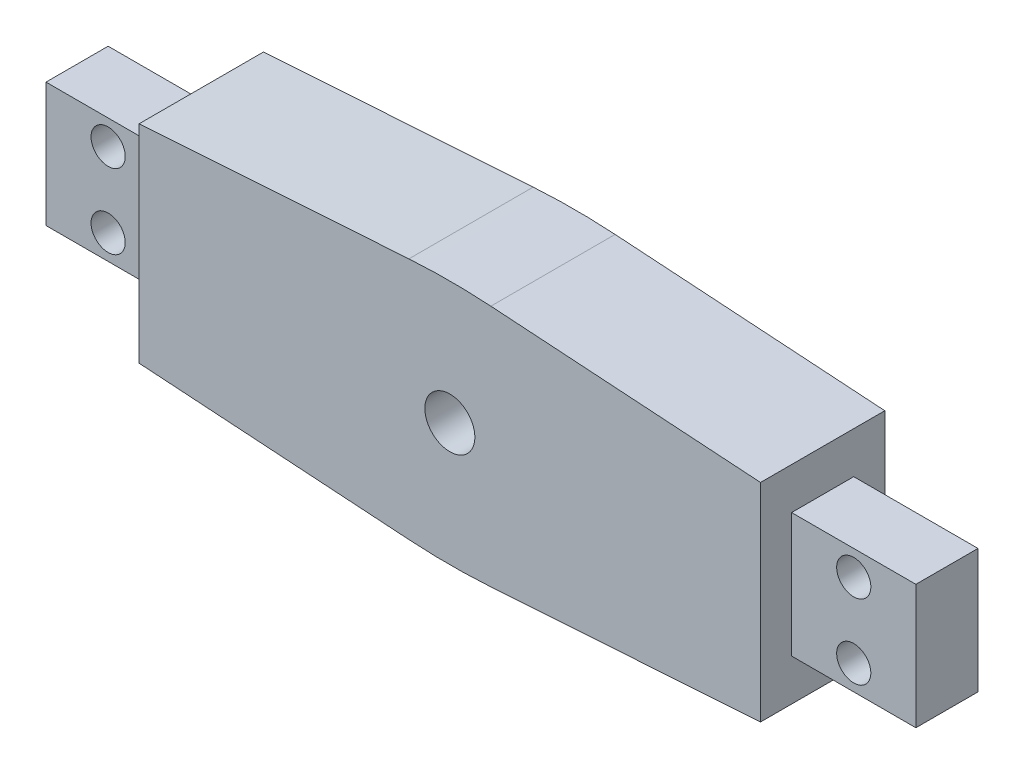
SolidWorks part; units mm, degrees
ref_plane "Front Plane" through (0, 0, 0) normal (0, 0, 1) x (1, 0, 0)
ref_plane "Top Plane" through (0, 0, 0) normal (0, 1, 0) x (1, 0, 0)
ref_plane "Right Plane" through (0, 0, 0) normal (1, 0, 0) x (0, 0, -1)
sketch "Sketch1" plane through (0, 0, 0) normal (0, 0, 1) x (1, 0, 0)
  line L0 (0, 0) -> (-50000, 0) construction
  line L1 (0, -20) -> (151.3167, -10) construction
  line L2 (0, 20) -> (151.3167, 10) construction
  line L3 (0, 0) -> (0, 50000) construction
  line L4 (122.4484, -204.4828) -> (119.5098, 130.5043) construction
  line L5 (0, -20) -> (-151.3167, -10) construction
  line L6 (0, 20) -> (-151.3167, 10) construction
  line L7 (50, 16.6957) -> (50, -16.6957)
  line L8 (50, 16.6957) -> (0, 20)
  line L9 (0, -20) -> (50, -16.6957)
  line L10 (0, -20) -> (-50, -16.6957)
  line L11 (-50, 16.6957) -> (-50, -16.6957)
  line L12 (-50, 16.6957) -> (0, 20)
  circle A1 centre (0, 0) radius 4.025
  arc A2 (-151.3167, -10) -> (-151.3167, 10) centre (-150.6558, 0) ccw construction
  arc A3 (151.3167, -10) -> (151.3167, 10) centre (150.6558, 0) cw construction
  dimension "D1" = 40
  dimension "D2" = 8.05
  dimension "D3" = 20
  dimension "D4" = 30
  dimension "D5" = 50
extrude "Boss-Extrude1" add sketch "Sketch1" along normal blind 20
fillet "Fillet1" radius 100 2 edges at (0, 20, 10) (0, -20, 10)
sketch "Sketch2" plane through (50, 0, 0) normal (1, 0, 0) x (0, 0, -1)
  line L1 (-15, 10) -> (-5, 10)
  line L2 (-15, 10) -> (-15, -10)
  line L3 (-15, -10) -> (-5, -10)
  line L4 (0, -16.6957) -> (0, 16.6957)
  line L5 (-20, -16.6957) -> (0, -16.6957)
  line L6 (-20, 16.6957) -> (-20, -16.6957)
  line L7 (0, 16.6957) -> (-20, 16.6957)
  line L8 (0, -16.6957) -> (0, 16.6957)
  line L9 (-20, -16.6957) -> (0, -16.6957)
  line L10 (-20, 16.6957) -> (-20, -16.6957)
  line L11 (0, 16.6957) -> (-20, 16.6957)
  line L12 (-5, 10) -> (-5, -10)
  line L13 (-15, 10) -> (-5, -10) construction
  line L14 (-15, -10) -> (-5, 10) construction
  point P2 (-10, 0)
  point P10 (-10, -16.6957)
  dimension "D2" = 10
  dimension "D3" = 20
  dimension "D1" = 0
extrude "Boss-Extrude2" add sketch "Sketch2" along normal blind 20 contours L12 L1 L2 L3
mirror "Mirror1" about plane through (0, 0, 0) normal (1, 0, 0) of "Boss-Extrude2"
sketch "Sketch3" plane through (0, 0, 5) normal (0, 0, -1) x (-1, 0, 0)
  circle A0 centre (60, -6) radius 2.75 construction
  circle A1 centre (60, 6) radius 2.75 construction
  circle A2 centre (-60, -6) radius 2.75 construction
  circle A3 centre (-60, 6) radius 2.75 construction
  circle A4 centre (60, -6) radius 2.75
  circle A5 centre (60, 6) radius 2.75
  circle A6 centre (-60, -6) radius 2.75
  circle A7 centre (-60, 6) radius 2.75
extrude "Cut-Extrude1" cut sketch "Sketch3" against normal through all
